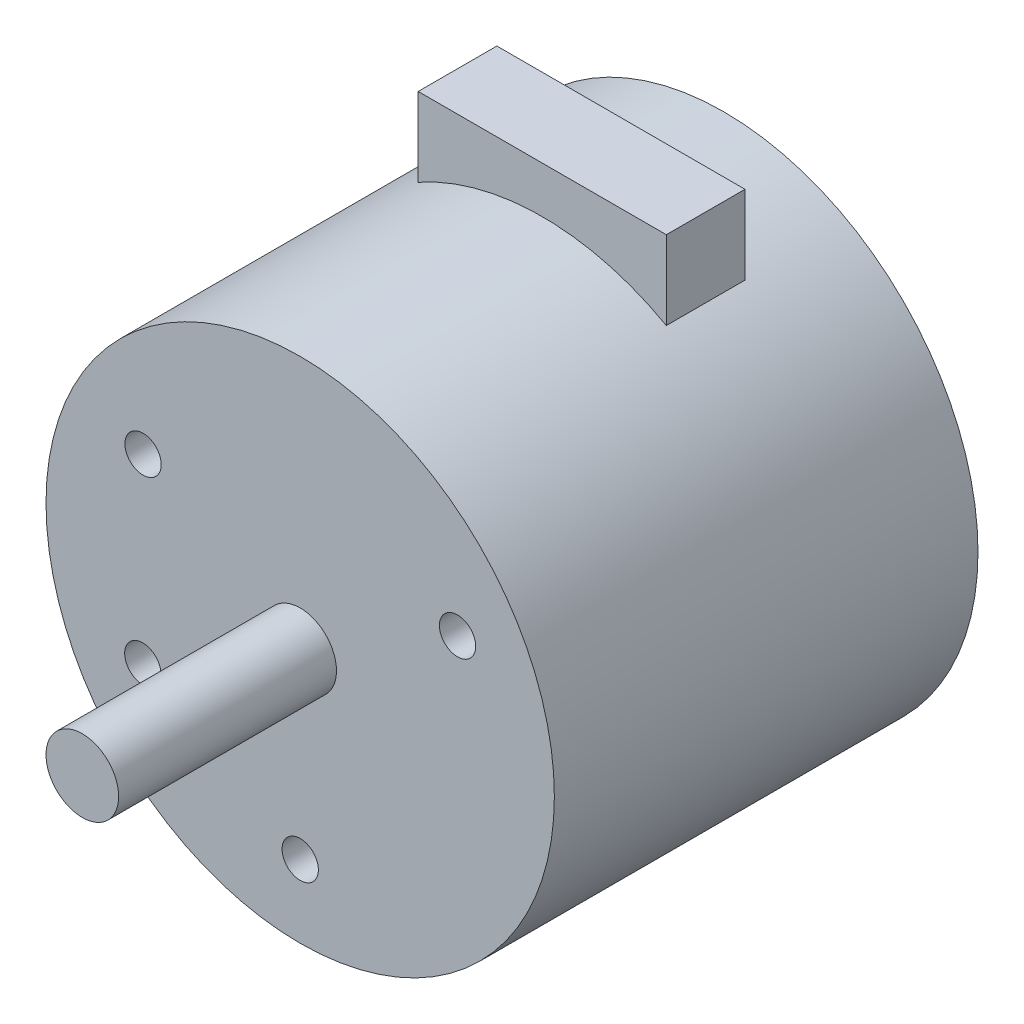
SolidWorks part; units mm, degrees
ref_plane "前视基准面" through (0, 0, 0) normal (0, 0, 1) x (1, 0, 0)
ref_plane "上视基准面" through (0, 0, 0) normal (0, 1, 0) x (1, 0, 0)
ref_plane "右视基准面" through (0, 0, 0) normal (1, 0, 0) x (0, 0, -1)
sketch "草图1" plane through (0, 0, 0) normal (0, 0, 1) x (1, 0, 0)
  circle A0 centre (0, 0) radius 21
  dimension "D1" = 42
extrude "凸台-拉伸1" add sketch "草图1" along normal blind 35
sketch "草图2" plane through (0, 0, 35) normal (0, 0, 1) x (1, 0, 0)
  circle A0 centre (0, 0) radius 3
  dimension "D1" = 6
extrude "凸台-拉伸2" add sketch "草图2" along normal blind 18
ref_plane "基准面1" through (0, 0, 15) normal (0, 0, -1) x (-1, 0, 0)
sketch "草图6" plane through (0, 0, 15) normal (0, 0, -1) x (-1, 0, 0)
  line L2 (-10.25, 18.3286) -> (-10.25, 24.8286)
  line L3 (-10.25, 24.8286) -> (10.25, 24.8286)
  line L4 (10.25, 18.3286) -> (10.25, 24.8286)
  line L5 (8.0134, 19.4109) -> (10.25, 24.8286) construction
  line L6 (-10.25, 24.8286) -> (-8.0134, 19.4109) construction
  arc A0 (-10.25, 18.3286) -> (10.25, 18.3286) centre (0, 0) cw
  circle A1 centre (0, 0) radius 21 construction
  point P0 (0, 0)
  dimension "D1" = 20.5
  dimension "D2" = 6.5
extrude "凸台-拉伸4" add sketch "草图6" along normal blind 6.5
sketch "草图7" plane through (0, 0, 35) normal (0, 0, 1) x (1, 0, 0)
  line L0 (0.0072, 0.0042) -> (13, 7.5) construction
  line L1 (-13, 7.5) -> (13, 7.5) construction
  line L2 (-13, 7.5) -> (-13, -7.5) construction
  line L3 (-13, -7.5) -> (13, -7.5) construction
  line L4 (13, 7.5) -> (13, -7.5) construction
  line L5 (-13, 7.5) -> (13, -7.5) construction
  line L6 (-13, -7.5) -> (13, 7.5) construction
  line L7 (0.0072, 0.0042) -> (0.0072, 11.072) construction
  circle A0 centre (13, 7.5) radius 1.5
  circle A1 centre (0.0024, -14.9958) radius 1.5
  circle A2 centre (-12.9808, 7.5083) radius 1.5
  circle A3 centre (-13, -7.5) radius 1.5
  point P0 (0, 0)
  dimension "D3" = 3
  dimension "D1" = 26
  dimension "D2" = 15
  dimension "D5" = 15
  dimension "D6" = 60.018
  dimension "D4" = 3
extrude "切除-拉伸1" cut sketch "草图7" against normal blind 6.5
hole_wizard "大小mm Press 暗销孔1" positions "草图8" profile "草图9" hole size "Ø3.0" standard "ISO" end condition through all
sketch "草图8" plane through (19.7778, 155.4337, 28.5) normal (0, 0, 1) x (0.2426, -0.9701, 0)
  point P0 (141.8694, -42.4664)
sketch "草图9" plane through (13, 7.5, 28.5) normal (1, 0, 0) x (0, -1, 0)
  line L0 (0, 0) -> (0, 28.5)
  line L1 (0, 28.5) -> (1.5, 28.5)
  line L2 (1.5, 28.5) -> (1.5, 0)
  line L3 (1.5, 0) -> (0, 0)
  line L4 (0, 110) -> (0, -10) construction
  dimension "Diameter" = 3
  dimension "Depth" = 28.5
hole_wizard "大小mm Press 暗销孔2" positions "草图10" profile "草图11" hole size "Ø3.0" standard "ISO" end condition through all
sketch "草图10" plane through (19.7778, 155.4337, 28.5) normal (0, 0, 1) x (0.2426, -0.9701, 0)
  point P0 (150.1132, -71.3288)
sketch "草图11" plane through (-13, -7.5, 28.5) normal (1, 0, 0) x (0, -1, 0)
  line L0 (0, 0) -> (0, 28.5)
  line L1 (0, 28.5) -> (1.5, 28.5)
  line L2 (1.5, 28.5) -> (1.5, 0)
  line L3 (1.5, 0) -> (0, 0)
  line L4 (0, -6.35) -> (0, 107.95) construction
  dimension "通孔孔直径" = 3
  dimension "通孔孔深度" = 28.5
